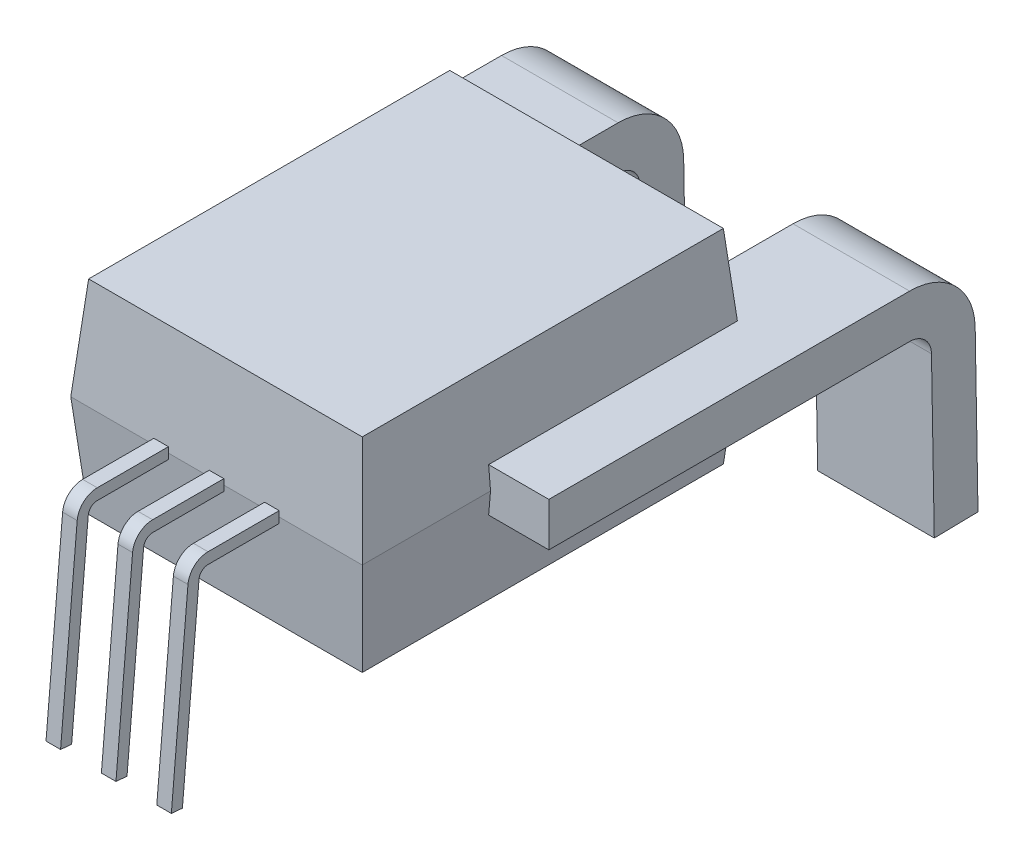
SolidWorks part; units mm, degrees
ref_plane "Front Plane" through (0, 0, 0) normal (0, 0, 1) x (1, 0, 0)
ref_plane "Top Plane" through (0, 0, 0) normal (0, 1, 0) x (1, 0, 0)
ref_plane "Right Plane" through (0, 0, 0) normal (1, 0, 0) x (0, 0, -1)
sketch "Sketch1" plane through (0, 0, 0) normal (0, 1, 0) x (1, 0, 0)
  line L1 (-5, -6.5) -> (5, -6.5)
  line L2 (-5, -6.5) -> (-5, 6.5)
  line L3 (-5, 6.5) -> (5, 6.5)
  line L4 (5, -6.5) -> (5, 6.5)
  line L5 (-5, -6.5) -> (5, 6.5) construction
  line L6 (-5, 6.5) -> (5, -6.5) construction
  point P0 (0, 0)
  dimension "D1" = 10
  dimension "D2" = 13
extrude "Extrude1" add sketch "Sketch1" along normal mid plane 7 draft 5
ref_plane "Plane1" through (5, 0, 0) normal (1, 0, 0) x (0, 0, -1)
ref_plane "Plane2" through (-5, 0, 0) normal (1, 0, 0) x (0, 0, -1)
ref_plane "Plane3" through (0, 0, 6.5) normal (0, 0, 1) x (1, 0, 0)
sketch "Sketch2" plane through (0, 0, 0) normal (1, 0, 0) x (0, 0, -1)
  line L0 (-6.5, 0) -> (-8.9418, 0)
  line L1 (-6.5, 3.85) -> (-6.5, -3.85) construction
  line L2 (-9.4399, -0.4564) -> (-10.0101, -6.9734)
  arc A1 (-8.9418, 0) -> (-9.4399, -0.4564) centre (-8.9418, -0.5) ccw
  point P8 (-9.4, 0)
  dimension "D5" = 0.5
  dimension "D1" = 7
  dimension "D2" = 2.9
  dimension "D3" = 95
sketch "Sketch3" plane through (0, 0, 6.5) normal (0, 0, 1) x (1, 0, 0)
  line L0 (1.65, -0.1905) -> (1.65, 0.1905)
  line L1 (1.65, 0.1905) -> (2.15, 0.1905)
  line L2 (-0.25, -0.1905) -> (0.25, -0.1905)
  line L3 (-0.25, -0.1905) -> (-0.25, 0.1905)
  line L4 (-0.25, 0.1905) -> (0.25, 0.1905)
  line L5 (0.25, -0.1905) -> (0.25, 0.1905)
  line L6 (-0.25, -0.1905) -> (0.25, 0.1905) construction
  line L7 (-0.25, 0.1905) -> (0.25, -0.1905) construction
  line L8 (2.15, -0.1905) -> (2.15, 0.1905)
  line L9 (1.65, -0.1905) -> (2.15, -0.1905)
  line L10 (-2.15, 0.1905) -> (-1.65, 0.1905)
  line L11 (-1.65, -0.1905) -> (-1.65, 0.1905)
  line L12 (-2.15, -0.1905) -> (-1.65, -0.1905)
  line L13 (-6.9, 0) -> (3.1, 0) construction
  line L14 (-2.15, -0.1905) -> (-2.15, 0.1905)
  line L15 (-5, 0) -> (5, 0) construction
  line L16 (-5, 0) -> (5, 0) construction
  line L17 (0, -0.1887) -> (0, 0.3429) construction
  point P1 (0, 0)
  dimension "D1" = 0.5
  dimension "D2" = 0.381
sweep "Sweep1" add profiles "Sketch3" path "Sketch2"
sketch "Sketch4" plane through (5, 0, 0) normal (1, 0, 0) x (0, 0, -1)
  line L0 (-6.5, 0) -> (-6.5, 5.9746) construction
  line L1 (-6.5, 5.5) -> (-6.5, -5.5) construction
  line L2 (-2.1, 0) -> (-2.1, 5.9746) construction
  line L3 (11, -8.0135) -> (11, 5.9746) construction
  line L4 (11.75, -8.0135) -> (11.75, 5.9746) construction
  line L5 (11, 0) -> (11, 5.9746) construction
  line L6 (11.75, 0) -> (11.75, 5.9746) construction
  line L7 (-2.1, 0) -> (10.276, 0)
  line L8 (11.7757, -1.4738) -> (11.8721, -6.9966)
  arc A0 (11.7757, -1.4738) -> (10.276, 0) centre (10.276, -1.5) ccw
  point P17 (11.75, 0)
  dimension "D6" = 1.5
  dimension "D4" = 6.9966
  dimension "D5" = 91
  dimension "D1" = 4.4
  dimension "D2" = 17.5
  dimension "D3" = 0.75
ref_plane "Plane4" through (0, 0, 2.1) normal (0, 0, 1) x (1, 0, 0)
sketch "Sketch5" plane through (0, 0, 2.1) normal (0, 0, 1) x (1, 0, 0)
  line L0 (0, 7.369) -> (0, -9.3854) construction
  line L1 (3, 0.75) -> (3, -0.75)
  line L2 (7, 0.75) -> (7, -0.75)
  line L3 (7.9137, 0) -> (2.7585, 0) construction
  line L4 (-5, 0) -> (5, 0) construction
  line L5 (7, 0.75) -> (3, 0.75)
  line L6 (7, -0.75) -> (3, -0.75)
  line L7 (3, 7.369) -> (3, -9.3854) construction
  line L8 (7.9137, 0.75) -> (2.7585, 0.75) construction
  line L9 (7.9137, -0.75) -> (2.7585, -0.75) construction
  line L10 (7, 7.369) -> (7, -9.3854) construction
  dimension "D5" = 4
  dimension "D6" = 0.75
  dimension "D1" = 3
  dimension "D2" = 4
  dimension "D3" = 0.75
  dimension "D4" = 0.75
sweep "Sweep2" add profiles "Sketch5" path "Sketch4"
mirror "Mirror1" about plane through (0, 0, 0) normal (1, 0, 0) of "Sweep2"
